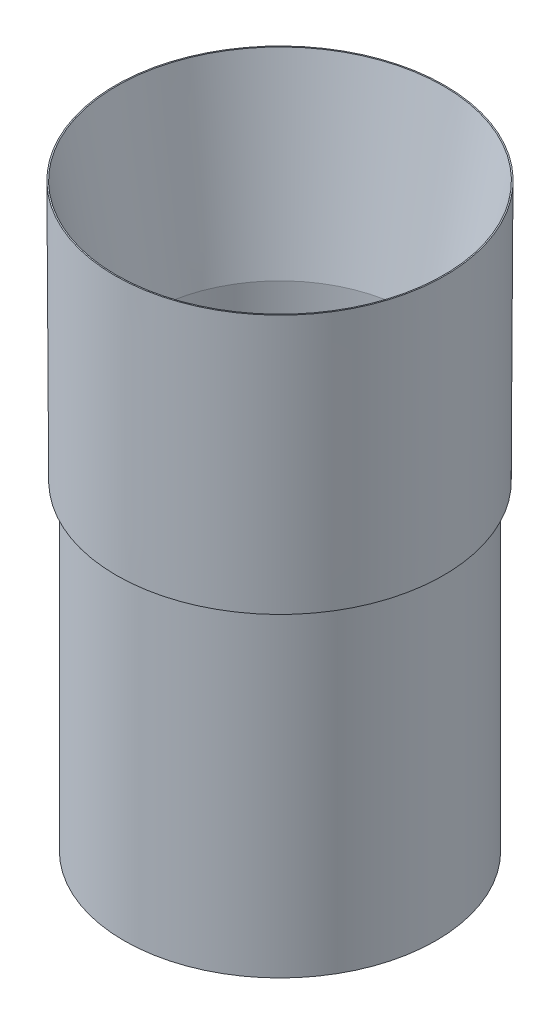
SolidWorks part; units mm, degrees
material "6061-T6 (SS)"
ref_plane "Front Plane" through (0, 0, 0) normal (0, 0, 1) x (1, 0, 0)
ref_plane "Top Plane" through (0, 0, 0) normal (0, 1, 0) x (1, 0, 0)
ref_plane "Right Plane" through (0, 0, 0) normal (1, 0, 0) x (0, 0, -1)
sketch "Sketch1" plane through (0, 0, 0) normal (0, 0, 1) x (1, 0, 0)
  line L0 (-49.53, 0) -> (-51.9176, 0)
  line L1 (-51.9176, 0) -> (-52.324, 82.549)
  line L2 (-52.324, 82.549) -> (-51.943, 82.549)
  line L3 (-51.943, 82.549) -> (-41.8661, 25.4)
  line L4 (-41.8661, 25.4) -> (-41.8661, 0)
  line L5 (-41.8661, 0) -> (-47.244, 0)
  line L6 (-47.244, 0) -> (-47.244, -101.6)
  line L7 (-47.244, -101.6) -> (-49.53, -101.6)
  line L8 (-49.53, -101.6) -> (-49.53, 0)
  line L9 (-51.943, 82.549) -> (-51.943, 25.4) construction
  line L10 (0, 0) -> (0, 82.549) construction
  line L11 (-52.324, 82.549) -> (-52.324, 0) construction
  dimension "D1" = 10
  dimension "D2" = 25.4
  dimension "D3" = 82.55
  dimension "D4" = 51.943
  dimension "D5" = 101.6
  dimension "D6" = 52.324
  dimension "D7" = 51.9176
  dimension "D8" = 49.53
  dimension "D9" = 2.286
revolve "Revolve1" add sketch "Sketch1" angle 360 about L10
